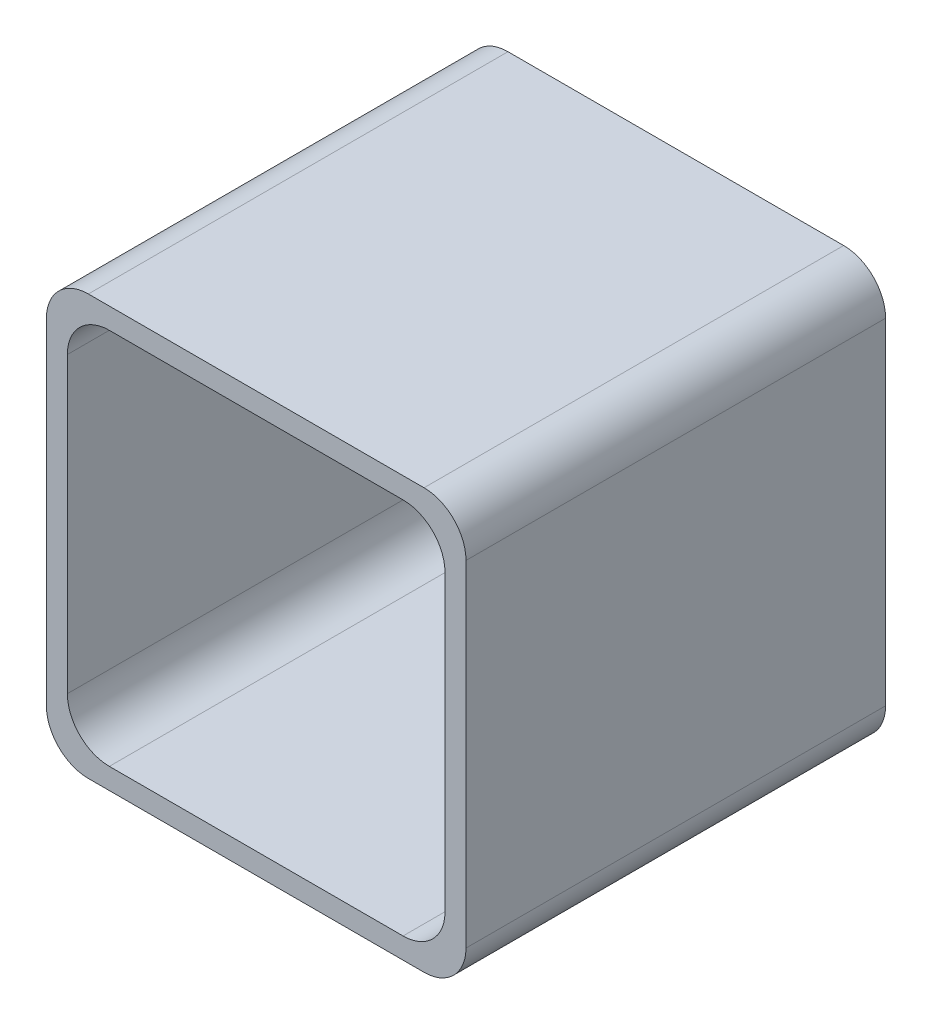
SolidWorks part; units mm, degrees
ref_plane "Front Plane" through (0, 0, 0) normal (0, 0, 1) x (1, 0, 0)
ref_plane "Top Plane" through (0, 0, 0) normal (0, 1, 0) x (1, 0, 0)
ref_plane "Right Plane" through (0, 0, 0) normal (1, 0, 0) x (0, 0, -1)
sketch "Sketch1" plane through (0, 0, 0) normal (0, 0, 1) x (1, 0, 0)
  line L1 (-25, -25) -> (25, -25)
  line L2 (-25, -25) -> (-25, 25)
  line L3 (-25, 25) -> (25, 25)
  line L4 (25, -25) -> (25, 25)
  line L5 (-25, -25) -> (25, 25) construction
  line L6 (-25, 25) -> (25, -25) construction
  point P0 (0, 0)
  point P6 (0, 0)
extrude "Boss-Extrude1" add sketch "Sketch1" against normal blind 50
sketch "Sketch3" plane through (0, 0, 0) normal (0, 0, 1) x (1, 0, 0)
  line L1 (-22.5, -22.5) -> (22.5, -22.5)
  line L2 (-22.5, -22.5) -> (-22.5, 22.5)
  line L3 (-22.5, 22.5) -> (22.5, 22.5)
  line L4 (22.5, -22.5) -> (22.5, 22.5)
  line L5 (-22.5, -22.5) -> (22.5, 22.5) construction
  line L6 (-22.5, 22.5) -> (22.5, -22.5) construction
  point P0 (0, 0)
extrude "Cut-Extrude4" cut sketch "Sketch3" against normal blind 45
sketch "Sketch5" plane through (0, 0, -45) normal (0, 0, 1) x (1, 0, 0)
  circle A0 centre (-14.5, 0) radius 3
  circle A1 centre (14.5, 0) radius 3
extrude "Boss-Extrude2" add sketch "Sketch5" along normal blind 8
hole_wizard "Tap Drill for M3x0.5 Tap2" positions "Sketch8" profile "Sketch9" hole size "M3x0.5" standard "ANSI Metric"
sketch "Sketch8" plane through (0, 0, -37) normal (0, 0, 1) x (1, 0, 0)
  point P0 (-14.5, 0)
  point P3 (14.5, 0)
sketch "Sketch9" plane through (-14.5, 0, -37) normal (1, 0, 0) x (0, -1, 0)
  line L0 (0, 0) -> (0, 8.7511)
  line L1 (0, 8.7511) -> (1.25, 8)
  line L2 (1.25, 8) -> (1.25, 0)
  line L5 (1.25, 0) -> (0, 0)
  line L10 (0, 8.7511) -> (-1.25, 8) construction
  line L11 (0, -6.35) -> (0, 107.95) construction
  dimension "Hole Dia." = 2.5
  dimension "Hole Depth" = 8
  dimension "Drill Angle" = 118
sketch "Sketch10" plane through (0, -22.5, 0) normal (0, 1, 0) x (1, 0, 0)
  circle A0 centre (0, 38.1846) radius 6
extrude "Cut-Extrude5" cut sketch "Sketch10" against normal blind 5
fillet "Fillet2" radius 5 8 edges at (22.5, 22.5, -22.5) (22.5, -22.5, -22.5) (-22.5, 22.5, -22.5) (-22.5, -22.5, -22.5) (25, 25, -25) (25, -25, -25) (-25, -25, -25) (-25, 25, -25)
